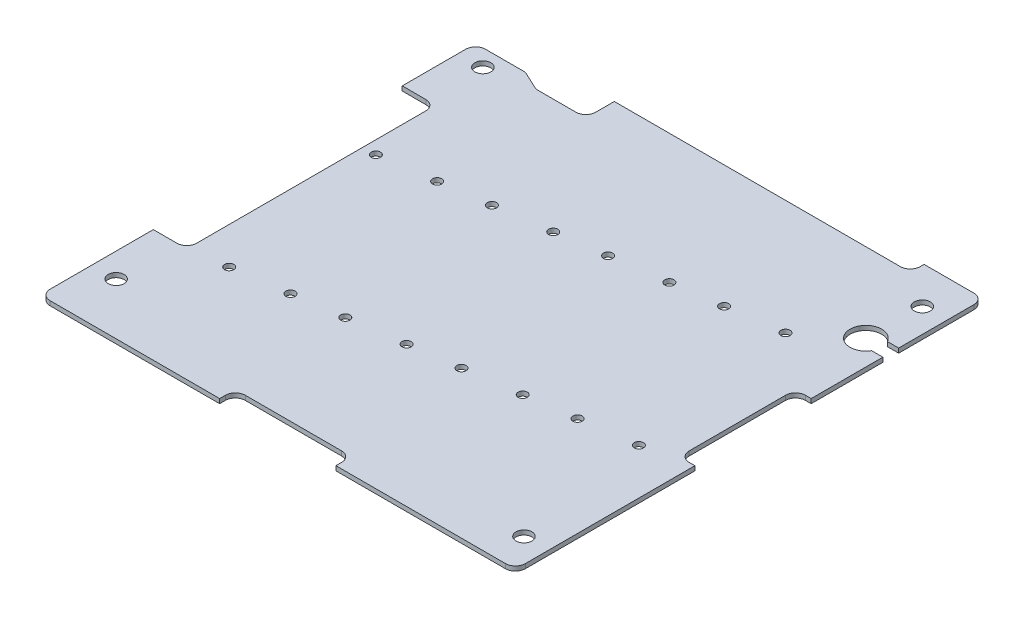
SolidWorks part; units mm, degrees
material "AISI 304"
ref_plane "Front Plane" through (0, 0, 0) normal (0, 0, 1) x (1, 0, 0)
ref_plane "Top Plane" through (0, 0, 0) normal (0, 1, 0) x (1, 0, 0)
ref_plane "Right Plane" through (0, 0, 0) normal (1, 0, 0) x (0, 0, -1)
sketch "Sketch2" plane through (0, 0, 0) normal (0, 1, 0) x (1, 0, 0)
  line L0 (78.2275, 86.065) -> (-5.1055, 86.065)
  line L1 (90.5925, 85.9634) -> (90.5925, 84.6934)
  line L2 (84.2425, 84.6934) -> (90.5925, 84.6934)
  line L3 (82.2275, 84.6934) -> (84.2425, 84.6934)
  line L4 (90.8305, 86.065) -> (82.8625, 86.065)
  line L5 (91.5925, -10.633) -> (91.5925, 85.303)
  line L6 (-5.1055, -11.395) -> (90.8305, -11.395)
  line L7 (-5.8675, 85.303) -> (-5.8675, -10.633)
  line L8 (14.2595, -9.744) -> (71.4655, -9.744)
  line L9 (89.9415, 65.938) -> (89.9415, 8.732)
  line L10 (77.5925, 84.4186) -> (18.4149, 84.4186)
  line L11 (-4.2165, 8.732) -> (-4.2165, 65.938)
  line L12 (29.3878, 73.268) -> (36.4998, 73.268)
  line L13 (69.3625, 82.9186) -> (75.6625, 82.9186)
  line L14 (39.7125, 82.9186) -> (46.0125, 82.9186)
  line L15 (20.3449, 82.9186) -> (26.6449, 82.9186)
  line L16 (-2.7165, 34.185) -> (-2.7165, 40.485)
  line L17 (46.0125, -8.244) -> (39.7125, -8.244)
  line L18 (11.2893, 76.1966) -> (12.6881, 76.1966)
  line L19 (9.69, 76.3922) -> (14.2874, 76.3922)
  line L20 (16.6363, 78.0686) -> (17.1449, 78.0686)
  line L21 (-2.6925, 78.0686) -> (-2.1839, 78.0686)
  line L22 (-2.1839, 78.0686) -> (16.6363, 78.0686)
  line L23 (88.4415, 40.485) -> (88.4415, 34.185)
  line L24 (17.1449, 78.0686) -> (17.1449, 86.065)
  line L25 (-2.6925, 78.0686) -> (-2.6925, 86.065)
  line L26 (18.4149, 84.4186) -> (18.4149, 86.065)
  line L27 (26.6449, 82.9186) -> (26.6449, 84.4186)
  line L28 (20.3449, 82.9186) -> (20.3449, 84.4186)
  line L29 (46.0125, 82.9186) -> (46.0125, 84.4186)
  line L30 (39.7125, 82.9186) -> (39.7125, 84.4186)
  line L31 (69.3625, 82.9186) -> (69.3625, 84.4186)
  line L32 (75.6625, 82.9186) -> (75.6625, 84.4186)
  line L33 (77.5925, 84.4186) -> (77.5925, 86.065)
  line L34 (89.9415, 65.938) -> (91.5925, 65.938)
  line L35 (88.4415, 40.485) -> (89.9415, 40.485)
  line L36 (29.3878, 73.268) -> (29.3878, 84.4186)
  line L37 (36.4998, 73.268) -> (36.4998, 84.4186)
  line L38 (14.2874, 76.3922) -> (14.2874, 78.0686)
  line L39 (9.69, 76.3922) -> (9.69, 78.0686)
  line L40 (-4.2165, 65.938) -> (-5.8675, 65.938)
  line L41 (-2.7165, 40.485) -> (-4.2165, 40.485)
  line L42 (-2.7165, 34.185) -> (-4.2165, 34.185)
  line L43 (-4.2165, 8.732) -> (-5.8675, 8.732)
  line L44 (14.2595, -9.744) -> (14.2595, -11.395)
  line L45 (39.7125, -8.244) -> (39.7125, -9.744)
  line L46 (46.0125, -8.244) -> (46.0125, -9.744)
  line L47 (71.4655, -9.744) -> (71.4655, -11.395)
  line L48 (88.4415, 34.185) -> (89.9415, 34.185)
  line L49 (89.9415, 8.732) -> (91.5925, 8.732)
  line L50 (-2.7165, 37.335) -> (-1.7165, 37.335) construction
  line L51 (-1.7165, 62.335) -> (-0.1465, 62.335) construction
  line L52 (-1.7165, 62.335) -> (-1.7165, 12.335) construction
  line L53 (-1.7165, 12.335) -> (-0.1465, 12.335) construction
  line L54 (-0.1465, 62.335) -> (-0.1465, 12.335) construction
  line L55 (-0.1465, 62.335) -> (0.8535, 62.335) construction
  line L56 (0.8535, 62.335) -> (0.8535, 12.335) construction
  line L57 (0.8535, 12.335) -> (-0.1465, 12.335) construction
  line L58 (-5.8675, 48.01) -> (-4.2165, 48.01)
  line L59 (-5.8675, 26.66) -> (-4.2165, 26.66)
  line L60 (32.1875, -9.744) -> (32.1875, -11.395)
  line L61 (53.5375, -9.744) -> (53.5375, -11.395)
  line L62 (89.9415, 48.01) -> (91.5925, 48.01)
  line L63 (89.9415, 26.66) -> (91.5925, 26.66)
  arc A0 (-5.1055, 86.065) -> (-5.8675, 85.303) centre (-5.1055, 85.303) ccw
  arc A1 (79.4482, 85.6464) -> (78.2275, 86.065) centre (78.2275, 84.0758) ccw
  arc A2 (79.4482, 85.6464) -> (82.2275, 84.6934) centre (82.2275, 89.2226) ccw
  arc A3 (91.5925, 85.303) -> (90.8305, 86.065) centre (90.8305, 85.303) ccw
  arc A4 (-5.8675, -10.633) -> (-5.1055, -11.395) centre (-5.1055, -10.633) ccw
  circle A5 centre (85.725, -3.81) radius 2.095
  circle A6 centre (0, 0) radius 2.095
  circle A7 centre (0, 73.66) radius 2.095
  circle A8 centre (85.725, 76.2) radius 2.095
  arc A9 (90.8305, -11.395) -> (91.5925, -10.633) centre (90.8305, -10.633) ccw
  point P106 (42.8625, -8.244)
  point P107 (88.4415, 37.335)
  dimension "D1" = 4.19
  dimension "D2" = 0.762
  dimension "D3" = 1.9892
  dimension "D4" = 4.5292
  dimension "D5" = 9.69
  dimension "D6" = 11.2893
  dimension "D7" = 12.6881
  dimension "D8" = 14.2595
  dimension "D9" = 14.2874
  dimension "D10" = 16.6363
  dimension "D11" = 17.1449
  dimension "D12" = 18.4149
  dimension "D13" = 20.3449
  dimension "D14" = 26.6449
  dimension "D15" = 29.3878
  dimension "D16" = 36.4998
  dimension "D17" = 39.7125
  dimension "D18" = 69.3625
  dimension "D19" = 71.4655
  dimension "D20" = 77.5925
  dimension "D21" = 78.2275
  dimension "D22" = 79.4482
  dimension "D23" = 82.8625
  dimension "D24" = 84.2425
  dimension "D25" = 85.725
  dimension "D26" = 88.4415
  dimension "D27" = 89.9415
  dimension "D28" = 90.5925
  dimension "D29" = 91.5925
  dimension "D30" = 2.1839
  dimension "D31" = 4.2165
  dimension "D32" = 5.8675
  dimension "D33" = 8.732
  dimension "D34" = 34.185
  dimension "D35" = 73.268
  dimension "D36" = 73.66
  dimension "D37" = 76.1966
  dimension "D38" = 76.2
  dimension "D39" = 76.3922
  dimension "D40" = 78.0686
  dimension "D41" = 82.9186
  dimension "D42" = 84.0758
  dimension "D43" = 84.4186
  dimension "D44" = 85.9634
  dimension "D45" = 3.81
  dimension "D46" = 8.244
  dimension "D47" = 9.744
  dimension "D48" = 1.5
  dimension "D49" = 1.57
  dimension "D50" = 50
  dimension "D51" = 1
  dimension "D52" = 1
  dimension "D53" = 21.35
  dimension "D54" = 10.675
  dimension "D55" = 21.35
  dimension "D56" = 10.675
  dimension "D57" = 21.35
  dimension "D58" = 10.675
sketch "Sketch6" plane through (0, 0, 0) normal (0, 1, 0) x (1, 0, 0)
  line L0 (-4.8675, 77.0686) -> (-4.8675, 62.335)
  line L1 (-4.8675, 62.335) -> (1.8535, 62.335)
  line L2 (1.8535, 62.335) -> (1.8535, 12.335)
  line L3 (1.8535, 12.335) -> (-4.8675, 12.335)
  line L4 (-4.8675, 12.335) -> (-4.8675, -10.395)
  line L5 (-4.8675, -10.395) -> (31.1875, -10.395)
  line L6 (31.1875, -10.395) -> (31.1875, -7.244)
  line L7 (31.1875, -7.244) -> (54.5375, -7.244)
  line L8 (54.5375, -7.244) -> (54.5375, -10.395)
  line L9 (54.5375, -10.395) -> (90.5925, -10.395)
  line L10 (90.5925, -10.395) -> (90.5925, 25.66)
  line L11 (90.5925, 25.66) -> (87.4415, 25.66)
  line L12 (87.4415, 25.66) -> (87.4415, 49.01)
  line L13 (87.4415, 49.01) -> (90.5925, 49.01)
  line L14 (90.5925, 49.01) -> (90.5925, 83.6934)
  line L15 (90.5925, 83.6934) -> (78.5925, 83.6934)
  line L16 (78.5925, 83.6934) -> (78.5925, 80.9186)
  line L17 (78.5925, 80.9186) -> (19.1449, 80.9186)
  line L18 (19.1449, 80.9186) -> (19.1449, 75.1966)
  line L19 (19.1449, 75.1966) -> (9.1325, 75.1966)
  line L20 (9.1325, 75.1966) -> (5.1325, 77.0686)
  line L21 (5.1325, 77.0686) -> (-4.8675, 77.0686)
  line L22 (-5.8675, 85.303) -> (-5.8675, -10.633) construction
  line L23 (-5.1055, -11.395) -> (90.8305, -11.395) construction
  line L24 (91.5925, -10.633) -> (91.5925, 85.303) construction
  line L25 (84.2425, 84.6934) -> (90.5925, 84.6934) construction
  line L26 (17.1449, 78.0686) -> (17.1449, 86.065) construction
  line L27 (11.2893, 76.1966) -> (12.6881, 76.1966) construction
  line L28 (-1.7165, 62.335) -> (-0.1465, 62.335) construction
  line L30 (-1.7165, 12.335) -> (-0.1465, 12.335) construction
  line L31 (32.1875, -9.744) -> (32.1875, -11.395) construction
  line L32 (53.5375, -9.744) -> (53.5375, -11.395) construction
  line L33 (89.9415, 26.66) -> (91.5925, 26.66) construction
  line L34 (89.9415, 48.01) -> (91.5925, 48.01) construction
  line L35 (39.7125, 82.9186) -> (46.0125, 82.9186) construction
  line L36 (88.4415, 40.485) -> (88.4415, 34.185) construction
  line L37 (46.0125, -8.244) -> (39.7125, -8.244) construction
  line L38 (0.8535, 62.335) -> (0.8535, 12.335) construction
  line L40 (77.5925, 84.4186) -> (77.5925, 86.065) construction
  line L41 (-2.1839, 78.0686) -> (16.6363, 78.0686) construction
  circle A0 centre (0, 73.66) radius 1.6
  circle A1 centre (85.725, 76.2) radius 1.6
  circle A2 centre (0, 0) radius 1.6
  circle A3 centre (85.725, -3.81) radius 1.6
  dimension "D18" = 3.2
  dimension "D1" = 1
  dimension "D2" = 1
  dimension "D3" = 1
  dimension "D4" = 1
  dimension "D5" = 1
  dimension "D6" = 1
  dimension "D7" = 1
  dimension "D8" = 1
  dimension "D9" = 2
  dimension "D10" = 1
  dimension "D11" = 1
  dimension "D12" = 2
  dimension "D13" = 1
  dimension "D14" = 1
  dimension "D15" = 1
  dimension "D16" = 10
  dimension "D17" = 14
  dimension "D19" = 1
extrude "Extrude1" add sketch "Sketch6" along normal blind 0.9
fillet "Fillet1" radius 2 14 edges at (9.1325, 0.45, -75.1966) (5.1325, 0.45, -77.0686) (-4.8675, 0.45, -77.0686) (78.5925, 0.45, -80.9186) (87.4415, 0.45, -49.01) (87.4415, 0.45, -25.66) (31.1875, 0.45, 7.244) (54.5375, 0.45, 7.244) (1.8535, 0.45, -12.335) (1.8535, 0.45, -62.335) (19.1449, 0.45, -75.1966) (-4.8675, 0.45, 10.395) (90.5925, 0.45, 10.395) (90.5925, 0.45, -83.6934)
sketch "Sketch7" plane through (0, 0.9, 0) normal (0, 1, 0) x (1, 0, 0)
  circle A0 centre (0, 73.66) radius 3.5
  circle A1 centre (85.725, 76.2) radius 3.5
  circle A2 centre (85.725, -3.81) radius 3.5
  circle A3 centre (0, 0) radius 3.5
  dimension "D1" = 7
sketch "Sketch9" plane through (0, 0, 0) normal (0, -1, 0) x (1, 0, 0)
  circle A1 centre (4.4546, -47.7057) radius 0.925
  circle A2 centre (4.4546, -47.7057) radius 0.925
  circle A3 centre (15.2485, -49.2227) radius 0.925
  circle A4 centre (15.2485, -49.2227) radius 0.925
  circle A5 centre (9.2699, -13.4424) radius 0.925
  circle A6 centre (9.2699, -13.4424) radius 0.925
  circle A7 centre (20.0639, -14.9594) radius 0.925
  circle A8 centre (20.0639, -14.9594) radius 0.925
  circle A9 centre (29.719, -16.3163) radius 0.925
  circle A10 centre (29.719, -16.3163) radius 0.925
  circle A11 centre (24.9036, -50.5796) radius 0.925
  circle A12 centre (24.9036, -50.5796) radius 0.925
  circle A13 centre (35.6975, -52.0966) radius 0.925
  circle A14 centre (35.6975, -52.0966) radius 0.925
  circle A15 centre (40.5129, -17.8333) radius 0.925
  circle A16 centre (40.5129, -17.8333) radius 0.925
  circle A17 centre (50.168, -19.1903) radius 0.925
  circle A18 centre (50.168, -19.1903) radius 0.925
  circle A19 centre (45.3526, -53.4535) radius 0.925
  circle A20 centre (45.3526, -53.4535) radius 0.925
  circle A21 centre (56.1466, -54.9705) radius 0.925
  circle A22 centre (56.1466, -54.9705) radius 0.925
  circle A23 centre (60.9619, -20.7073) radius 0.925
  circle A24 centre (60.9619, -20.7073) radius 0.925
  circle A25 centre (65.8017, -56.3275) radius 0.925
  circle A26 centre (65.8017, -56.3275) radius 0.925
  circle A27 centre (70.6171, -22.0642) radius 0.925
  circle A28 centre (70.6171, -22.0642) radius 0.925
  circle A29 centre (81.411, -23.5812) radius 0.925
  circle A30 centre (81.411, -23.5812) radius 0.925
  circle A31 centre (76.5956, -57.8445) radius 0.925
  circle A32 centre (76.5956, -57.8445) radius 0.925
  dimension "D1" = 0
  dimension "D2" = 0
  dimension "D3" = 0
  dimension "D4" = 0
  dimension "D5" = 0
  dimension "D6" = 0
  dimension "D7" = 0
  dimension "D8" = 0
  dimension "D9" = 0
  dimension "D10" = 0
  dimension "D11" = 0
  dimension "D12" = 0
  dimension "D13" = 0
  dimension "D14" = 0
  dimension "D15" = 0
  dimension "D16" = 0
extrude "Cut-Extrude1" cut sketch "Sketch9" against normal through all
sketch "Sketch11" plane through (0, 0.9, 0) normal (0, 1, 0) x (1, 0, 0)
  line L3 (88.3421, 63.4125) -> (90.5925, 63.4125)
  line L4 (90.5925, 66.5875) -> (88.3421, 66.5875)
  line L5 (90.5925, 63.4125) -> (90.5925, 66.5875)
  line L6 (88.3421, 63.4125) -> (90.5925, 63.4125)
  line L7 (90.5925, 66.5875) -> (88.3421, 66.5875)
  line L8 (90.5925, 63.4125) -> (90.5925, 66.5875)
  arc A1 (88.3421, 66.5875) -> (88.3421, 63.4125) centre (85.5925, 65) ccw
  arc A2 (88.3421, 66.5875) -> (88.3421, 63.4125) centre (85.5925, 65) ccw
  dimension "D1" = 0
extrude "Cut-Extrude2" cut sketch "Sketch11" against normal through all
sketch "Sketch12" plane through (0, 0.9, 0) normal (0, 1, 0) x (1, 0, 0)
  line L25 (90.5925, 63.4125) -> (88.3421, 63.4125)
  line L26 (88.3421, 66.5875) -> (90.5925, 66.5875)
  line L27 (90.5925, 66.5875) -> (90.5925, 81.6934)
  line L28 (88.5925, 83.6934) -> (78.5925, 83.6934)
  line L29 (78.5925, 83.6934) -> (78.5925, 82.9186)
  line L30 (76.5925, 80.9186) -> (19.1449, 80.9186)
  line L31 (19.1449, 80.9186) -> (19.1449, 77.1966)
  line L32 (17.1449, 75.1966) -> (9.5774, 75.1966)
  line L33 (8.7296, 75.3851) -> (5.5354, 76.88)
  line L34 (4.6876, 77.0686) -> (-2.8675, 77.0686)
  line L35 (-4.8675, 75.0686) -> (-4.8675, 62.335)
  line L36 (-4.8675, 62.335) -> (-0.1465, 62.335)
  line L37 (1.8535, 60.335) -> (1.8535, 14.335)
  line L38 (-0.1465, 12.335) -> (-4.8675, 12.335)
  line L39 (-4.8675, 12.335) -> (-4.8675, -8.395)
  line L40 (-2.8675, -10.395) -> (31.1875, -10.395)
  line L41 (31.1875, -10.395) -> (31.1875, -9.244)
  line L42 (33.1875, -7.244) -> (52.5375, -7.244)
  line L43 (54.5375, -9.244) -> (54.5375, -10.395)
  line L44 (54.5375, -10.395) -> (88.5925, -10.395)
  line L45 (90.5925, -8.395) -> (90.5925, 25.66)
  line L46 (90.5925, 25.66) -> (89.4415, 25.66)
  line L47 (87.4415, 27.66) -> (87.4415, 47.01)
  line L48 (89.4415, 49.01) -> (90.5925, 49.01)
  line L49 (90.5925, 49.01) -> (90.5925, 63.4125)
  line L50 (90.5925, 63.4125) -> (88.3421, 63.4125)
  line L51 (88.3421, 66.5875) -> (90.5925, 66.5875)
  line L52 (90.5925, 66.5875) -> (90.5925, 81.6934)
  line L53 (88.5925, 83.6934) -> (78.5925, 83.6934)
  line L54 (78.5925, 83.6934) -> (78.5925, 82.9186)
  line L55 (76.5925, 80.9186) -> (19.1449, 80.9186)
  line L56 (19.1449, 80.9186) -> (19.1449, 77.1966)
  line L57 (17.1449, 75.1966) -> (9.5774, 75.1966)
  line L58 (8.7296, 75.3851) -> (5.5354, 76.88)
  line L59 (4.6876, 77.0686) -> (-2.8675, 77.0686)
  line L60 (-4.8675, 75.0686) -> (-4.8675, 62.335)
  line L61 (-4.8675, 62.335) -> (-0.1465, 62.335)
  line L62 (1.8535, 60.335) -> (1.8535, 14.335)
  line L63 (-0.1465, 12.335) -> (-4.8675, 12.335)
  line L64 (-4.8675, 12.335) -> (-4.8675, -8.395)
  line L65 (-2.8675, -10.395) -> (31.1875, -10.395)
  line L66 (31.1875, -10.395) -> (31.1875, -9.244)
  line L67 (33.1875, -7.244) -> (52.5375, -7.244)
  line L68 (54.5375, -9.244) -> (54.5375, -10.395)
  line L69 (54.5375, -10.395) -> (88.5925, -10.395)
  line L70 (90.5925, -8.395) -> (90.5925, 25.66)
  line L71 (90.5925, 25.66) -> (89.4415, 25.66)
  line L72 (87.4415, 27.66) -> (87.4415, 47.01)
  line L73 (89.4415, 49.01) -> (90.5925, 49.01)
  line L74 (90.5925, 49.01) -> (90.5925, 63.4125)
  circle A0 centre (85.725, 76.2) radius 1.6 construction
  circle A1 centre (0, 73.66) radius 1.6 construction
  circle A2 centre (0, 0) radius 1.6 construction
  circle A3 centre (85.725, -3.81) radius 1.6 construction
  circle A4 centre (85.725, 76.2) radius 1.6
  circle A5 centre (0, 73.66) radius 1.6
  circle A6 centre (0, 0) radius 1.6
  circle A7 centre (85.725, -3.81) radius 1.6
  circle A8 centre (4.4546, 47.7057) radius 0.925 construction
  circle A9 centre (15.2485, 49.2227) radius 0.925 construction
  circle A10 centre (24.9036, 50.5796) radius 0.925 construction
  circle A11 centre (35.6975, 52.0966) radius 0.925 construction
  circle A12 centre (45.3526, 53.4535) radius 0.925 construction
  circle A13 centre (56.1466, 54.9705) radius 0.925 construction
  circle A14 centre (65.8017, 56.3275) radius 0.925 construction
  arc A15 (88.3421, 66.5875) -> (88.3421, 63.4125) centre (85.5925, 65) ccw
  arc A16 (90.5925, 81.6934) -> (88.5925, 83.6934) centre (88.5925, 81.6934) ccw
  arc A17 (76.5925, 80.9186) -> (78.5925, 82.9186) centre (76.5925, 82.9186) ccw
  arc A18 (17.1449, 75.1966) -> (19.1449, 77.1966) centre (17.1449, 77.1966) ccw
  arc A19 (8.7296, 75.3851) -> (9.5774, 75.1966) centre (9.5774, 77.1966) ccw
  arc A20 (5.5354, 76.88) -> (4.6876, 77.0686) centre (4.6876, 75.0686) ccw
  arc A21 (-2.8675, 77.0686) -> (-4.8675, 75.0686) centre (-2.8675, 75.0686) ccw
  arc A22 (1.8535, 60.335) -> (-0.1465, 62.335) centre (-0.1465, 60.335) ccw
  arc A23 (-0.1465, 12.335) -> (1.8535, 14.335) centre (-0.1465, 14.335) ccw
  arc A24 (-4.8675, -8.395) -> (-2.8675, -10.395) centre (-2.8675, -8.395) ccw
  arc A25 (33.1875, -7.244) -> (31.1875, -9.244) centre (33.1875, -9.244) ccw
  arc A26 (54.5375, -9.244) -> (52.5375, -7.244) centre (52.5375, -9.244) ccw
  arc A27 (88.5925, -10.395) -> (90.5925, -8.395) centre (88.5925, -8.395) ccw
  arc A28 (87.4415, 27.66) -> (89.4415, 25.66) centre (89.4415, 27.66) ccw
  arc A29 (89.4415, 49.01) -> (87.4415, 47.01) centre (89.4415, 47.01) ccw
  arc A30 (88.3421, 66.5875) -> (88.3421, 63.4125) centre (85.5925, 65) ccw
  arc A31 (90.5925, 81.6934) -> (88.5925, 83.6934) centre (88.5925, 81.6934) ccw
  arc A32 (76.5925, 80.9186) -> (78.5925, 82.9186) centre (76.5925, 82.9186) ccw
  arc A33 (17.1449, 75.1966) -> (19.1449, 77.1966) centre (17.1449, 77.1966) ccw
  arc A34 (8.7296, 75.3851) -> (9.5774, 75.1966) centre (9.5774, 77.1966) ccw
  arc A35 (5.5354, 76.88) -> (4.6876, 77.0686) centre (4.6876, 75.0686) ccw
  arc A36 (-2.8675, 77.0686) -> (-4.8675, 75.0686) centre (-2.8675, 75.0686) ccw
  arc A37 (1.8535, 60.335) -> (-0.1465, 62.335) centre (-0.1465, 60.335) ccw
  arc A38 (-0.1465, 12.335) -> (1.8535, 14.335) centre (-0.1465, 14.335) ccw
  arc A39 (-4.8675, -8.395) -> (-2.8675, -10.395) centre (-2.8675, -8.395) ccw
  arc A40 (33.1875, -7.244) -> (31.1875, -9.244) centre (33.1875, -9.244) ccw
  arc A41 (54.5375, -9.244) -> (52.5375, -7.244) centre (52.5375, -9.244) ccw
  arc A42 (88.5925, -10.395) -> (90.5925, -8.395) centre (88.5925, -8.395) ccw
  arc A43 (87.4415, 27.66) -> (89.4415, 25.66) centre (89.4415, 27.66) ccw
  arc A44 (89.4415, 49.01) -> (87.4415, 47.01) centre (89.4415, 47.01) ccw
  circle A45 centre (76.5956, 57.8445) radius 0.925 construction
  circle A46 centre (9.2699, 13.4424) radius 0.925 construction
  circle A47 centre (20.0639, 14.9594) radius 0.925 construction
  circle A48 centre (29.719, 16.3163) radius 0.925 construction
  circle A49 centre (40.5129, 17.8333) radius 0.925 construction
  circle A50 centre (50.168, 19.1903) radius 0.925 construction
  circle A51 centre (60.9619, 20.7073) radius 0.925 construction
  circle A52 centre (70.6171, 22.0642) radius 0.925 construction
  circle A53 centre (81.411, 23.5812) radius 0.925 construction
  circle A54 centre (4.4546, 47.7057) radius 0.925
  circle A55 centre (15.2485, 49.2227) radius 0.925
  circle A56 centre (24.9036, 50.5796) radius 0.925
  circle A57 centre (35.6975, 52.0966) radius 0.925
  circle A58 centre (45.3526, 53.4535) radius 0.925
  circle A59 centre (56.1466, 54.9705) radius 0.925
  circle A60 centre (65.8017, 56.3275) radius 0.925
  circle A61 centre (76.5956, 57.8445) radius 0.925
  circle A62 centre (9.2699, 13.4424) radius 0.925
  circle A63 centre (20.0639, 14.9594) radius 0.925
  circle A64 centre (29.719, 16.3163) radius 0.925
  circle A65 centre (40.5129, 17.8333) radius 0.925
  circle A66 centre (50.168, 19.1903) radius 0.925
  circle A67 centre (60.9619, 20.7073) radius 0.925
  circle A68 centre (70.6171, 22.0642) radius 0.925
  circle A69 centre (81.411, 23.5812) radius 0.925
  dimension "D1" = 0
